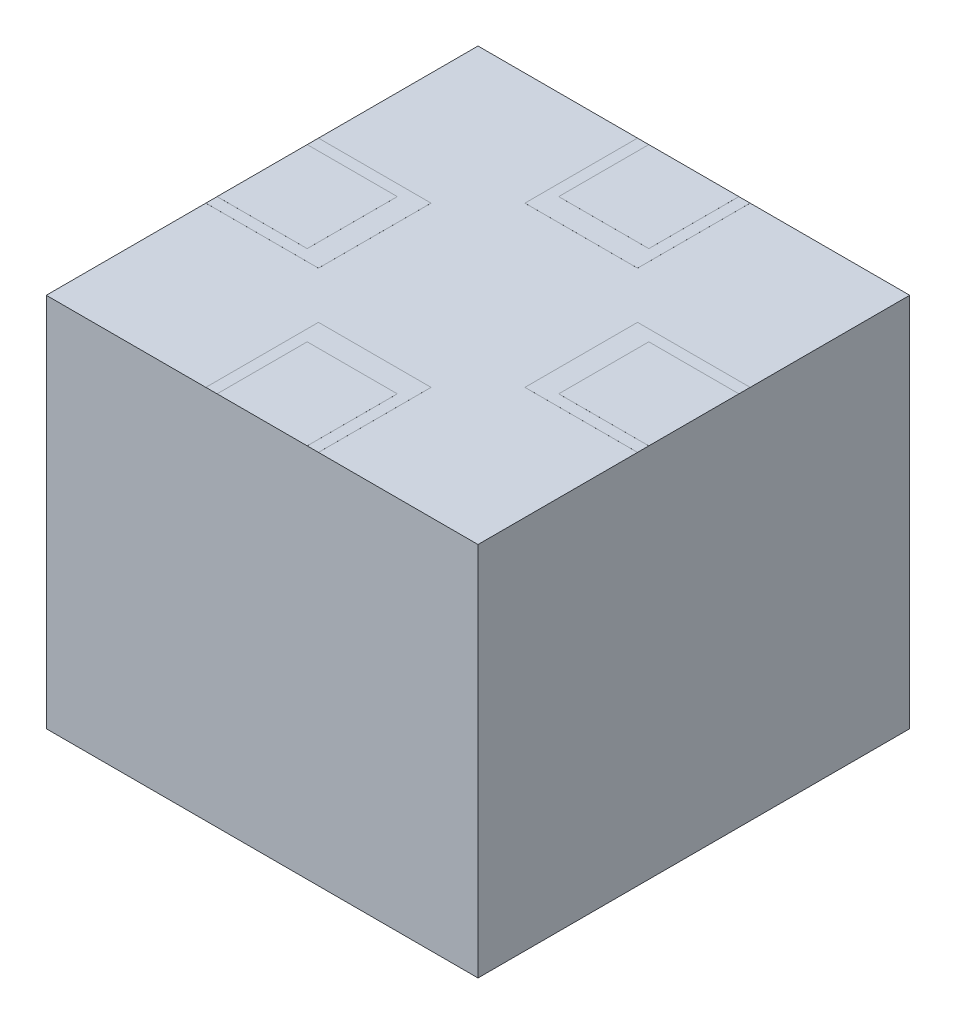
SolidWorks part; units mm, degrees
ref_plane "Front Plane" through (0, 0, 0) normal (0, 0, 1) x (1, 0, 0)
ref_plane "Top Plane" through (0, 0, 0) normal (0, 1, 0) x (1, 0, 0)
ref_plane "Right Plane" through (0, 0, 0) normal (1, 0, 0) x (0, 0, -1)
sketch "Sketch1" plane through (0, 0, 0) normal (0, 1, 0) x (1, 0, 0)
  line L5 (-115, -115) -> (115, -115)
  line L6 (-115, -115) -> (-115, 115)
  line L7 (-115, 115) -> (115, 115)
  line L8 (115, -115) -> (115, 115)
  line L9 (-115, -115) -> (115, 115) construction
  line L10 (-115, 115) -> (115, -115) construction
  point P0 (0, 0)
  dimension "D1" = 230
  dimension "D2" = 230
extrude "Boss-Extrude1" add sketch "Sketch1" along normal blind 200
sketch "Sketch3" plane through (0, 200, 0) normal (0, 1, 0) x (1, 0, 0)
  line L8 (55, 30) -> (55, -30)
  line L10 (115, 30) -> (55, 30)
  line L11 (-115, 115) -> (-115, -115) construction
  line L13 (-30, 115) -> (30, 115)
  line L17 (-30, 115) -> (-30, 55)
  line L18 (-30, 55) -> (30, 55)
  line L20 (30, 115) -> (30, 55)
  line L24 (-30, 115) -> (30, 55) construction
  line L25 (-30, 55) -> (30, 115) construction
  line L27 (115, 115) -> (-115, 115) construction
  line L34 (115, 30) -> (115, -30)
  line L35 (115, -30) -> (55, -30)
  line L36 (30, -55) -> (-30, -55)
  line L37 (30, -115) -> (30, -55)
  line L38 (30, -115) -> (-30, -115)
  line L39 (-30, -115) -> (-30, -55)
  line L40 (-55, -30) -> (-55, 30)
  line L41 (-115, -30) -> (-55, -30)
  line L42 (-115, -30) -> (-115, 30)
  line L43 (-115, 30) -> (-55, 30)
  line L44 (115, -115) -> (115, 115) construction
  point P0 (0, 85)
  point P9 (30, -85)
  point P24 (0, 0)
  dimension "D1" = 60
  dimension "D2" = 60
  dimension "D3" = 85
  dimension "D4" = 0
  dimension "D5" = 4
  dimension "D6" = 85
  dimension "D7" = 85
extrude "Boss-Extrude2" add sketch "Sketch3" along normal blind 0.01
sketch "Sketch5" plane through (0, 200.01, 0) normal (0, 1, 0) x (1, 0, 0)
  line L1 (30, 115) -> (-30, 115) construction
  line L3 (-24, 115) -> (-24, 67)
  line L4 (-24, 67) -> (24, 67)
  line L5 (24, 67) -> (24, 115)
  line L7 (-24, 115) -> (24, 115)
  line L10 (-115, 115) -> (-115, 30) construction
  line L11 (115, 24) -> (67, 24)
  line L12 (67, 24) -> (67, -24)
  line L13 (67, -24) -> (115, -24)
  line L14 (115, 24) -> (115, -24)
  line L15 (24, -115) -> (24, -67)
  line L16 (24, -67) -> (-24, -67)
  line L17 (-24, -67) -> (-24, -115)
  line L18 (24, -115) -> (-24, -115)
  line L19 (-115, -24) -> (-67, -24)
  line L20 (-67, -24) -> (-67, 24)
  line L21 (-67, 24) -> (-115, 24)
  line L22 (-115, -24) -> (-115, 24)
  line L23 (115, 115) -> (30, 115) construction
  line L24 (115, -115) -> (115, -30) construction
  point P23 (0, 0)
  dimension "D1" = 48
  dimension "D2" = 48
  dimension "D3" = 91
  dimension "D4" = 4
  dimension "D5" = 91
  dimension "D6" = 91
extrude "Boss-Extrude3" add sketch "Sketch5" along normal blind 0.01
